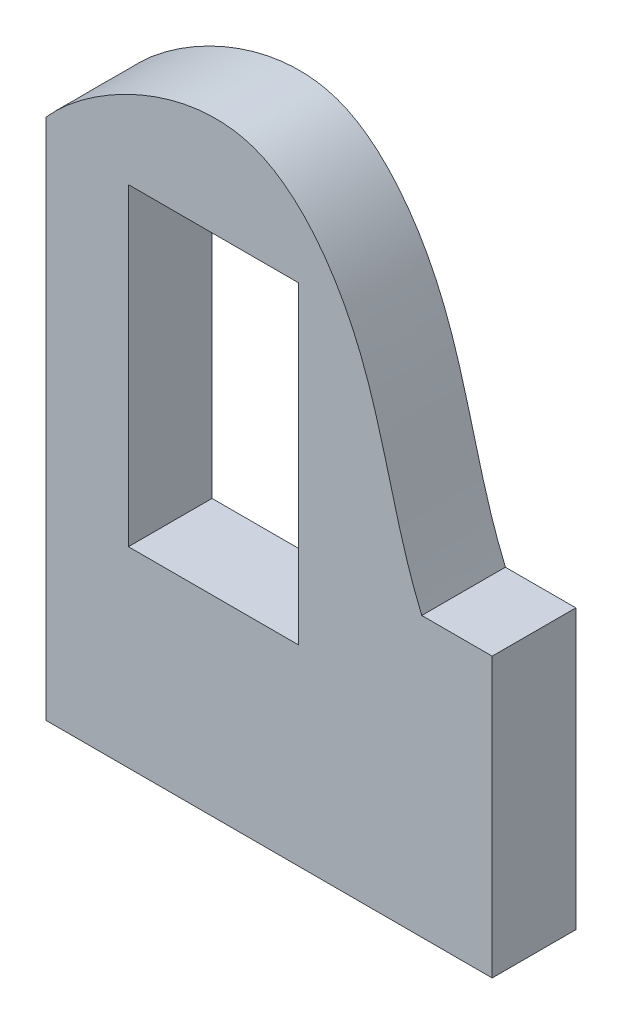
SolidWorks part; units mm, degrees
ref_plane "Front Plane" through (0, 0, 0) normal (0, 0, 1) x (1, 0, 0)
ref_plane "Top Plane" through (0, 0, 0) normal (0, 1, 0) x (1, 0, 0)
ref_plane "Right Plane" through (0, 0, 0) normal (1, 0, 0) x (0, 0, -1)
sketch "Sketch1" plane through (0, 0, 0) normal (0, 0, 1) x (1, 0, 0)
  line L0 (-32, 20) -> (-32, 55)
  line L1 (-32, -20) -> (32, -20)
  line L2 (-32, -20) -> (-32, 20)
  line L3 (-32, 20) -> (32, 20)
  line L4 (32, -20) -> (32, 20)
  line L5 (0, 20) -> (0, -20) construction
  line L6 (-32, 0) -> (32, 0) construction
  line L7 (21.8947, 20) -> (-32, 20)
  spline S0 degree 3 poles (-32, 55) (-26.0931, 61.8283) (-5.1033, 73.6425) (16.0622, 49.1007) (17.0609, 31.4035) (21.8947, 20) knots 0 0 0 0 0.38116 0.579099 1 1 1 1
  point P0 (0, 0)
  dimension "D1" = 64
  dimension "D2" = 40
  dimension "D3" = 35
extrude "Boss-Extrude1" add sketch "Sketch1" along normal blind 12 contours S0 L0 L3 | L1 L4 L3 L2
sketch "Sketch2" plane through (0, 0, 12) normal (0, 0, 1) x (1, 0, 0)
  line L0 (32, -20) -> (32, 20) construction
  line L1 (4.2, 52.5) -> (-20.2, 52.5)
  line L2 (4.2, 52.5) -> (4.2, 7.5)
  line L3 (4.2, 7.5) -> (-20.2, 7.5)
  line L4 (-20.2, 52.5) -> (-20.2, 7.5)
  line L5 (-8, 7.5) -> (-8, 52.5) construction
  line L6 (4.2, 30) -> (-20.2, 30) construction
  line L7 (-32, -20) -> (32, -20) construction
  point P0 (-8, 30)
  dimension "D1" = 40
  dimension "D2" = 45
  dimension "D3" = 50
  dimension "D4" = 24.4
extrude "Cut-Extrude1" cut sketch "Sketch2" against normal blind 20
